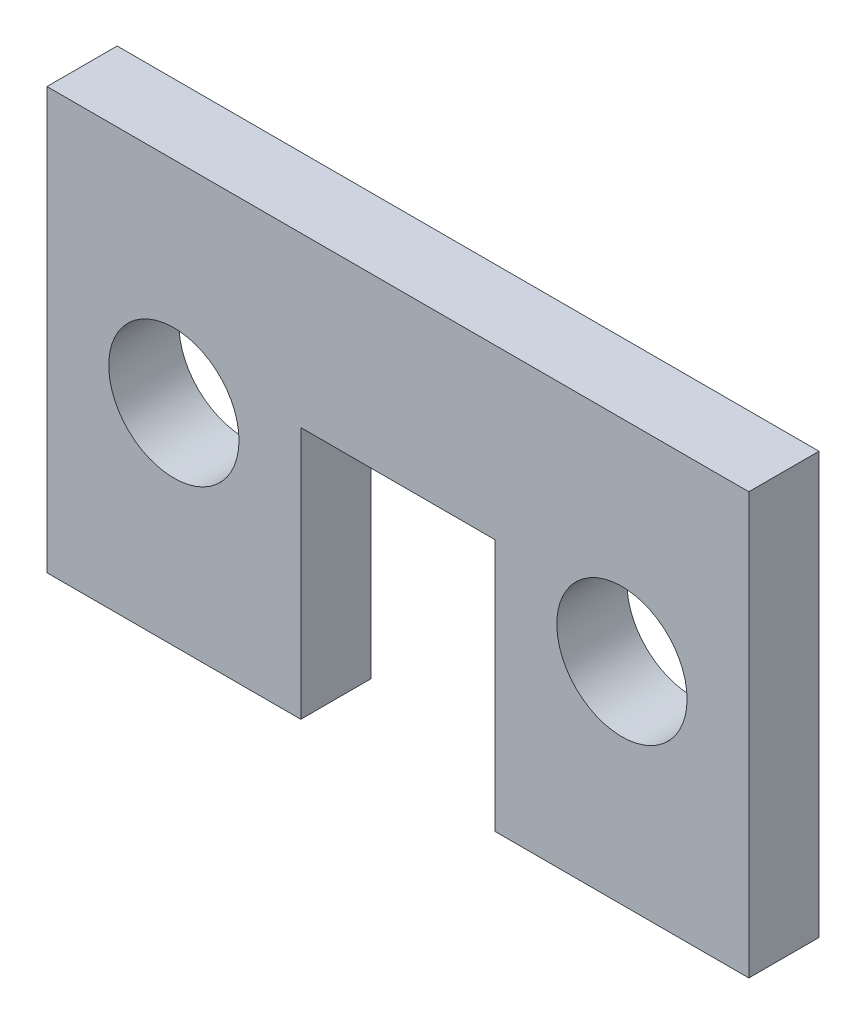
SolidWorks part; units mm, degrees
ref_plane "Front Plane" through (0, 0, 0) normal (0, 0, 1) x (1, 0, 0)
ref_plane "Top Plane" through (0, 0, 0) normal (0, 1, 0) x (1, 0, 0)
ref_plane "Right Plane" through (0, 0, 0) normal (1, 0, 0) x (0, 0, -1)
sketch "Sketch1" plane through (0, 0, 0) normal (0, 0, 1) x (1, 0, 0)
  line L1 (-2.1971, 2.8575) -> (2.1971, 2.8575)
  line L2 (-2.1971, 2.8575) -> (-2.1971, -2.8575)
  line L3 (-2.1971, -2.8575) -> (2.1971, -2.8575)
  line L4 (2.1971, 2.8575) -> (2.1971, -2.8575)
  line L5 (-2.1971, 2.8575) -> (2.1971, -2.8575) construction
  line L6 (-2.1971, -2.8575) -> (2.1971, 2.8575) construction
  point P0 (0, 0)
  dimension "D1" = 4.3942
  dimension "D2" = 5.715
sketch "Sketch2" plane through (0, 0, 0) normal (0, 0, 1) x (1, 0, 0)
  line L0 (-2.1971, 2.8575) -> (2.1971, 2.8575) construction
  line L1 (-2.1971, 2.8575) -> (-2.1971, -2.8575) construction
  line L2 (2.1971, 2.8575) -> (2.1971, -2.8575) construction
  line L3 (-2.1971, 2.8575) -> (2.1971, 2.8575)
  line L4 (-2.1971, 2.8575) -> (-2.1971, -2.8575)
  line L5 (2.1971, 2.8575) -> (2.1971, -2.8575)
  line L6 (-2.1971, -2.8575) -> (-7.9375, -2.8575)
  line L7 (-7.9375, -2.8575) -> (-7.9375, 6.6675)
  line L8 (-7.9375, 6.6675) -> (7.9375, 6.6675)
  line L9 (0, 0) -> (0, 11.1631) construction
  line L10 (-2.1971, 2.8575) -> (2.1971, -2.8575) construction
  line L11 (2.1971, -2.8575) -> (7.9375, -2.8575)
  line L12 (7.9375, -2.8575) -> (7.9375, 6.6675)
  point P13 (0, 6.6675)
  dimension "D1" = 15.875
  dimension "D2" = 9.525
extrude "Boss-Extrude1" add sketch "Sketch2" along normal blind 1.5875
hole_wizard "#4 Clearance Hole1" positions "Sketch5" profile "Sketch4" hole size "#4" standard "Ansi Inch" end condition through all
sketch "Sketch5" plane through (0, 0, 1.5875) normal (0, 0, 1) x (1, 0, 0)
  line L0 (-7.9375, 6.6675) -> (-7.9375, -2.8575) construction
  line L1 (7.9375, -2.8575) -> (7.9375, 6.6675) construction
  line L2 (2.1971, -2.8575) -> (7.9375, -2.8575) construction
  line L3 (-7.9375, -2.8575) -> (-2.1971, -2.8575) construction
  point P0 (-5.0673, 1.905)
  point P1 (5.0673, 1.905)
  point P10 (-7.9375, 1.905)
  point P13 (7.9375, 1.905)
  point P17 (5.0673, -2.8575)
  point P20 (-5.0673, -2.8575)
sketch "Sketch4" plane through (-5.0673, 1.905, 1.5875) normal (1, 0, 0) x (0, -1, 0)
  line L0 (0, 0) -> (0, 1.5875)
  line L1 (0, 1.5875) -> (1.4732, 1.5875)
  line L2 (1.4732, 1.5875) -> (1.4732, 0)
  line L5 (1.4732, 0) -> (0, 0)
  line L11 (0, -6.35) -> (0, 107.95) construction
  dimension "Thru Hole Dia." = 2.9464
  dimension "Thru Hole Depth" = 1.5875
